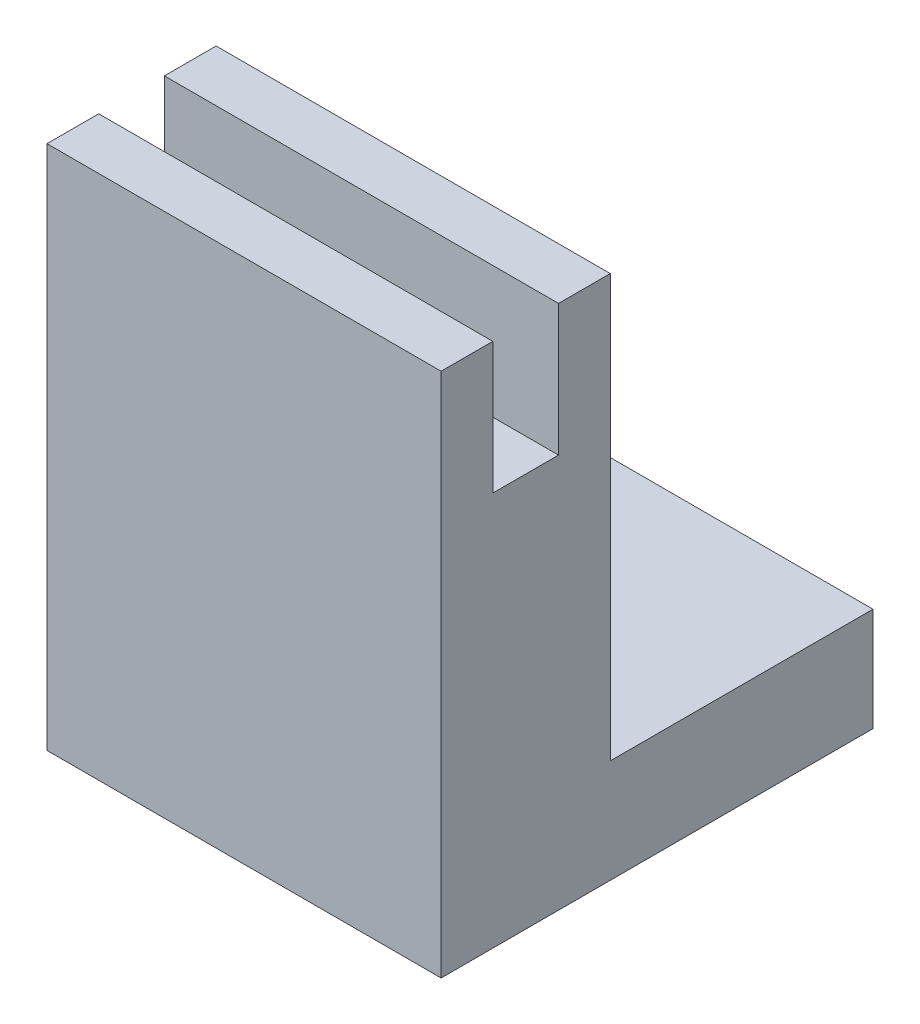
SolidWorks part; units mm, degrees
material "ABS"
ref_plane "Front Plane" through (0, 0, 0) normal (0, 0, 1) x (1, 0, 0)
ref_plane "Top Plane" through (0, 0, 0) normal (0, 1, 0) x (1, 0, 0)
ref_plane "Right Plane" through (0, 0, 0) normal (1, 0, 0) x (0, 0, -1)
sketch "Sketch1" plane through (0, 0, 0) normal (1, 0, 0) x (0, 0, -1)
  line L0 (0, 0) -> (41.75, 0)
  line L1 (41.75, 0) -> (41.75, 10)
  line L2 (41.75, 10) -> (16.35, 10)
  line L3 (16.35, 10) -> (16.35, 50.8)
  line L4 (16.35, 50.8) -> (11.35, 50.8)
  line L5 (11.35, 50.8) -> (11.35, 38.1)
  line L6 (11.35, 38.1) -> (5, 38.1)
  line L7 (5, 38.1) -> (5, 50.8)
  line L8 (5, 50.8) -> (0, 50.8)
  line L9 (0, 50.8) -> (0, 0)
  dimension "D1" = 6.35
  dimension "D2" = 5
  dimension "D3" = 5
  dimension "D4" = 10
  dimension "D5" = 25.4
  dimension "D6" = 12.7
  dimension "D7" = 0
  dimension "D8" = 38.1
extrude "Boss-Extrude1" add sketch "Sketch1" along normal blind 38.1
equation "\"D1@Sketch1\"=1in/4"
equation "\"D8@Sketch1\"=1.5in"
equation "\"D1@Boss-Extrude1\"=1.5in"
equation "\"D6@Sketch1\"=.5in"
equation "\"D5@Sketch1\"=1in"
